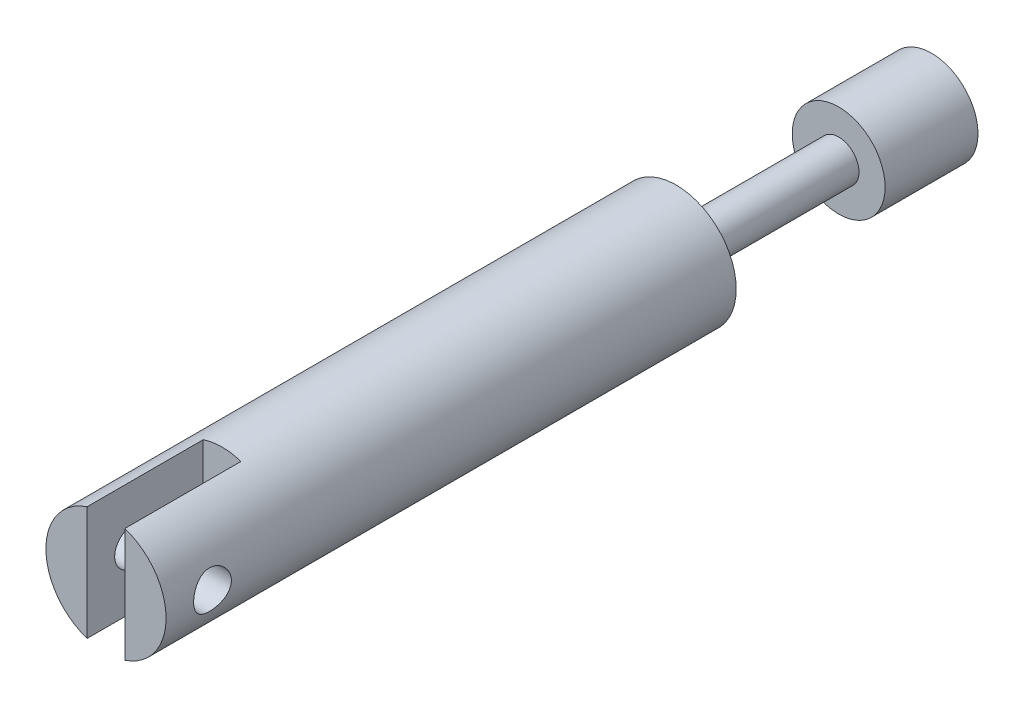
SolidWorks part; units mm, degrees
ref_plane "Front Plane" through (0, 0, 0) normal (0, 0, 1) x (1, 0, 0)
ref_plane "Top Plane" through (0, 0, 0) normal (0, 1, 0) x (1, 0, 0)
ref_plane "Right Plane" through (0, 0, 0) normal (1, 0, 0) x (0, 0, -1)
sketch "Sketch1" plane through (0, 0, 0) normal (1, 0, 0) x (0, 0, -1)
  line L1 (0, 0) -> (49.1, 0)
  line L2 (0, 0) -> (0, 5.175)
  line L3 (0, 5.175) -> (49.1, 5.175)
  line L4 (49.1, 0) -> (49.1, 5.175)
  line L5 (49.1, 0) -> (63.1, 0)
  line L6 (49.1, 0) -> (49.1, 1.75)
  line L7 (49.1, 1.75) -> (63.1, 1.75)
  line L8 (63.1, 0) -> (63.1, 1.75)
  line L9 (63.1, 0) -> (71.1, 0)
  line L10 (63.1, 0) -> (63.1, 4)
  line L11 (63.1, 4) -> (71.1, 4)
  line L12 (71.1, 0) -> (71.1, 4)
  dimension "D1" = 49.1
  dimension "D2" = 5.175
  dimension "D3" = 14
  dimension "D4" = 1.75
  dimension "D5" = 8
  dimension "D6" = 4
revolve "Revolve1" add sketch "Sketch1" angle 360 about L5
sketch "Sketch4" plane through (0, 0, 0) normal (0, 0, 1) x (1, 0, 0)
  line L1 (-1.625, -5.5) -> (1.625, -5.5)
  line L2 (-1.625, -5.5) -> (-1.625, 5.5)
  line L3 (-1.625, 5.5) -> (1.625, 5.5)
  line L4 (1.625, -5.5) -> (1.625, 5.5)
  line L5 (-1.625, -5.5) -> (1.625, 5.5) construction
  line L6 (-1.625, 5.5) -> (1.625, -5.5) construction
  point P0 (0, 0)
  dimension "D1" = 3.25
  dimension "D2" = 11
extrude "Cut-Extrude1" cut sketch "Sketch4" against normal blind 10
ref_plane "Plane1" through (5.175, 0, 0) normal (1, 0, 0) x (0, 0, -1)
sketch "Sketch5" plane through (5.175, 0, 0) normal (1, 0, 0) x (0, 0, -1)
  line L0 (0, 4.9132) -> (0, -4.9132) construction
  line L1 (49.1, 5.175) -> (10, 5.175) construction
  circle A0 centre (4, 0) radius 1.625
  dimension "D1" = 3.25
  dimension "D2" = 4
  dimension "D3" = 5.175
extrude "Cut-Extrude2" cut sketch "Sketch5" against normal blind 12
